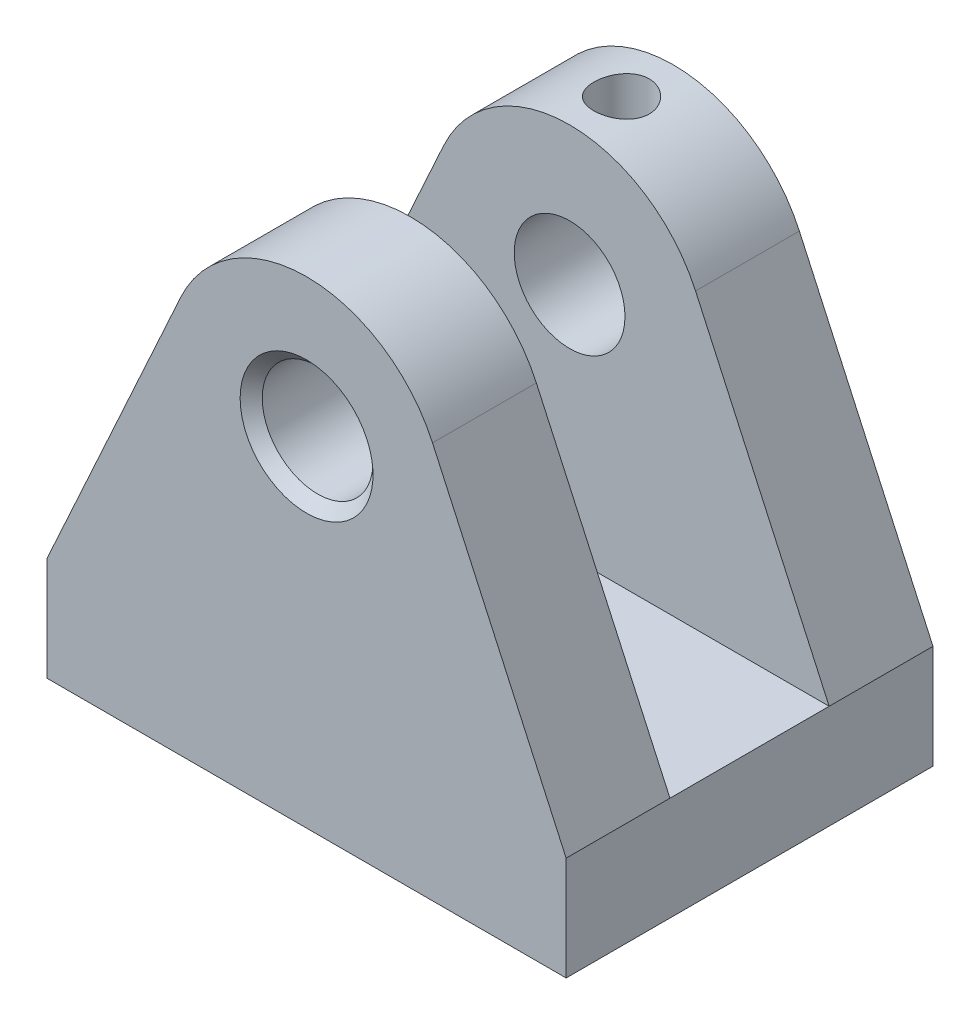
SolidWorks part; units mm, degrees
ref_plane "Přední rovina" through (0, 0, 0) normal (0, 0, 1) x (1, 0, 0)
ref_plane "Horní rovina" through (0, 0, 0) normal (0, 1, 0) x (1, 0, 0)
ref_plane "Pravá rovina" through (0, 0, 0) normal (1, 0, 0) x (0, 0, -1)
sketch "Skica1" plane through (0, 0, 0) normal (0, 0, 1) x (1, 0, 0)
  line L0 (0, 90.5038) -> (0, -6.0358) construction
  line L4 (-37.5, 0) -> (-37.5, 14.997)
  line L5 (-37.5, 14.997) -> (-18.1949, 57.3002)
  line L6 (37.5, 14.997) -> (18.1949, 57.3002)
  line L11 (0, -68.6488) -> (0, -75.939) construction
  line L12 (-37.5, 0) -> (37.5, 0)
  line L13 (37.5, 0) -> (37.5, 14.997)
  arc A1 (-18.1949, 57.3002) -> (18.1949, 57.3002) centre (0, 48.997) cw
  point P6 (0, 0)
  point P13 (0, 68.997)
  point P16 (0, 0)
  dimension "D2" = 20
  dimension "D1" = 14.997
  dimension "D3" = 75
  dimension "D4" = 54
extrude "Přidat vysunutím1" add sketch "Skica1" along normal blind 15 contours L5 A1 L6 L13 L12 L4
sketch "Skica4" plane through (0, 0, 0) normal (0, 0, -1) x (-1, 0, 0)
  line L0 (-37.5, 14.997) -> (-37.5, 0)
  line L1 (-37.5, 0) -> (37.5, 0)
  line L2 (37.5, 0) -> (37.5, 14.997)
  line L3 (37.5, 14.997) -> (-37.5, 14.997)
extrude "Přidat vysunutím2" add sketch "Skica4" along normal blind 11.5
ref_plane "Rovina1" through (0, 0, -11.5) normal (0, 0, 1) x (1, 0, 0)
ref_plane "Rovina2" through (0, 69, 0) normal (0, 1, 0) x (1, 0, 0)
mirror "Zrcadlit1" about plane through (0, 0, -11.5) normal (0, 0, 1) of bodies 105
sketch "Skica6" plane through (0, 0, 15) normal (0, 0, 1) x (1, 0, 0)
  line L0 (0, -6.8856) -> (0, 104.8856) construction
  circle A0 centre (0, 49) radius 8
  dimension "D1" = 16
  dimension "D2" = 49
extrude "Odebrat vysunutím1" cut sketch "Skica6" against normal through all
sketch "Skica7" plane through (0, 69, 0) normal (0, 1, 0) x (1, 0, 0)
  line L0 (0, -2.1399) -> (0, 41.1362) construction
  line L1 (18.1949, 38) -> (-18.1949, 38) construction
  circle A0 centre (0, 30.5) radius 4
  dimension "D1" = 8
  dimension "D2" = 7.5
extrude "Odebrat vysunutím2" cut sketch "Skica7" against normal up to next
cosmetic thread "Kosmetický závit1" parameters "D2"=10
chamfer "Zkosení1" distance 1.6 angle 45 2 edges at (8, 49, -38) (8, 49, 15)
